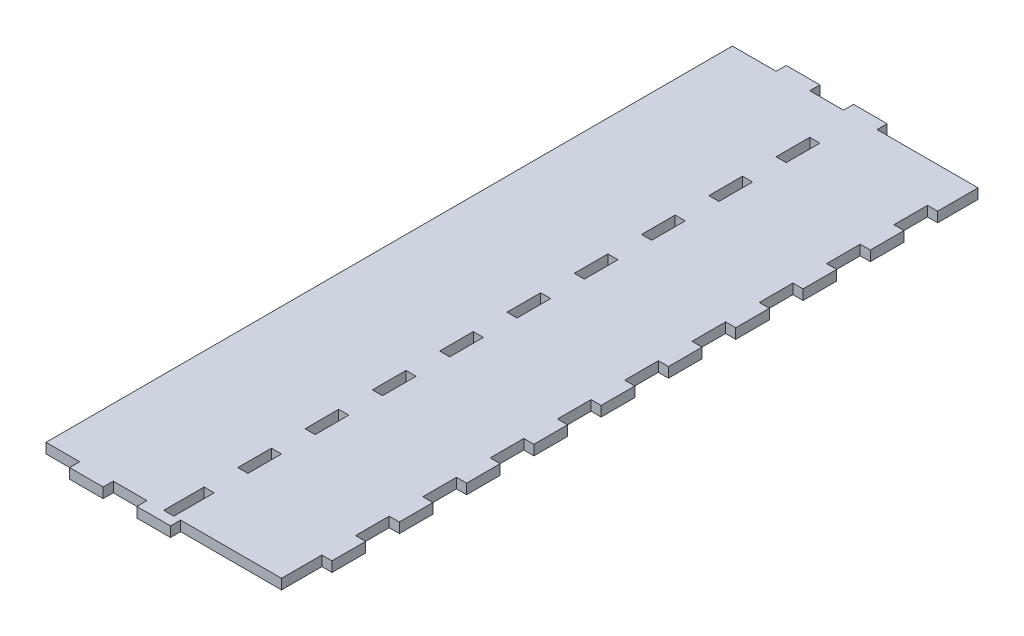
SolidWorks part; units mm, degrees
ref_plane "Front Plane" through (0, 0, 0) normal (0, 0, 1) x (1, 0, 0)
ref_plane "Top Plane" through (0, 0, 0) normal (0, 1, 0) x (1, 0, 0)
ref_plane "Right Plane" through (0, 0, 0) normal (1, 0, 0) x (0, 0, -1)
sketch "Sketch1" plane through (0, 0, 0) normal (0, 1, 0) x (1, 0, 0)
  line L1 (0, 0) -> (70, 0)
  line L2 (0, 0) -> (0, 204)
  line L3 (0, 204) -> (70, 204)
  line L4 (70, 0) -> (70, 204)
  dimension "D1" = 204
  dimension "D2" = 70
extrude "Boss-Extrude1" add sketch "Sketch1" along normal blind 3
sketch "Sketch2" plane through (70, 0, 0) normal (1, 0, 0) x (0, 0, -1)
  line L0 (0, 3) -> (204, 3) construction
  line L1 (204, 0) -> (192, 0)
  line L2 (204, 0) -> (204, 3)
  line L3 (204, 3) -> (192, 3)
  line L4 (192, 0) -> (192, 3)
  line L5 (0, 0) -> (204, 0) construction
  line L6 (182, 3) -> (172, 3)
  line L7 (182, 3) -> (182, 0)
  line L8 (182, 0) -> (172, 0)
  line L9 (172, 3) -> (172, 0)
  line L10 (162, 3) -> (162, 0)
  line L11 (162, 3) -> (152, 3)
  line L12 (152, 3) -> (152, 0)
  line L13 (162, 0) -> (152, 0)
  line L14 (142, 3) -> (142, 0)
  line L15 (142, 3) -> (132, 3)
  line L16 (132, 3) -> (132, 0)
  line L17 (142, 0) -> (132, 0)
  line L18 (122, 3) -> (122, 0)
  line L19 (122, 3) -> (112, 3)
  line L20 (112, 3) -> (112, 0)
  line L21 (122, 0) -> (112, 0)
  line L22 (102, 3) -> (102, 0)
  line L23 (102, 3) -> (92, 3)
  line L24 (92, 3) -> (92, 0)
  line L25 (102, 0) -> (92, 0)
  line L26 (82, 3) -> (82, 0)
  line L27 (82, 3) -> (72, 3)
  line L28 (72, 3) -> (72, 0)
  line L29 (82, 0) -> (72, 0)
  line L30 (62, 3) -> (62, 0)
  line L31 (62, 3) -> (52, 3)
  line L32 (52, 3) -> (52, 0)
  line L33 (62, 0) -> (52, 0)
  line L34 (42, 3) -> (42, 0)
  line L35 (42, 3) -> (32, 3)
  line L36 (32, 3) -> (32, 0)
  line L37 (42, 0) -> (32, 0)
  line L38 (22, 3) -> (22, 0)
  line L39 (22, 3) -> (12, 3)
  line L40 (12, 3) -> (12, 0)
  line L41 (22, 0) -> (12, 0)
  dimension "D1" = 12
  dimension "D2" = 10
  dimension "D3" = 10
  dimension "D4" = 9
extrude "Boss-Extrude2" add sketch "Sketch2" along normal blind 3
sketch "Esquisse4" plane through (0, 3, 0) normal (0, 1, 0) x (1, 0, 0)
  line L0 (73, 192) -> (70, 192) construction
  line L1 (35, 192) -> (38, 192)
  line L2 (35, 192) -> (35, 182)
  line L3 (35, 182) -> (38, 182)
  line L4 (38, 192) -> (38, 182)
  line L5 (73, 204) -> (0, 204) construction
  point P8 (36.5, 204)
  point P9 (36.5, 192)
  dimension "D1" = 3
  dimension "D2" = 10
extrude "Enlèv. mat.-Extru.3" cut sketch "Esquisse4" against normal through all
pattern_linear "Répétition linéaire2" count 10 spacing 20 along (0, 0, 1) of "Enlèv. mat.-Extru.3"
sketch "Esquisse5" plane through (0, 0, -2) normal (0, 0, -1) x (-1, 0, 0)
  line L0 (-38, 0) -> (-38, 3) construction
  line L1 (-38, 0) -> (-35, 0)
  line L2 (-38, 0) -> (-38, 3)
  line L3 (-38, 3) -> (-35, 3)
  line L4 (-35, 0) -> (-35, 3)
extrude "Enlèv. mat.-Extru.4" cut sketch "Esquisse5" against normal through all
sketch "Esquisse6" plane through (0, 0, 0) normal (0, 0, 1) x (1, 0, 0)
  line L0 (0, 0) -> (35, 0) construction
  line L1 (10, 0) -> (20, 0)
  line L2 (10, 0) -> (10, 3)
  line L3 (10, 3) -> (20, 3)
  line L4 (20, 0) -> (20, 3)
  line L5 (0, 3) -> (35, 3) construction
  line L6 (0, 3) -> (0, 0) construction
  line L7 (30, 0) -> (40, 0)
  line L8 (30, 0) -> (30, 3)
  line L9 (30, 3) -> (40, 3)
  line L10 (40, 0) -> (40, 3)
  line L16 (50, 0) -> (60, 0) [skipped]
  line L17 (50, 0) -> (50, 3) [skipped]
  line L18 (50, 3) -> (60, 3) [skipped]
  line L19 (60, 0) -> (60, 3) [skipped]
  dimension "D1" = 10
  dimension "D2" = 10
  dimension "D4" = 10
  dimension "D3" = 3
extrude "Boss.-Extru.1" add sketch "Esquisse6" along normal blind 3
sketch "Esquisse7" plane through (0, 0, -204) normal (0, 0, -1) x (-1, 0, 0)
  line L7 (-43, 0) -> (-33, 0)
  line L8 (-43, 0) -> (-43, 3)
  line L9 (-43, 3) -> (-33, 3)
  line L10 (-33, 0) -> (-33, 3)
  line L11 (-23, 0) -> (-13, 0)
  line L12 (-23, 0) -> (-23, 3)
  line L13 (-23, 3) -> (-13, 3)
  line L14 (-13, 0) -> (-13, 3)
  line L15 (0, 3) -> (0, 0) construction
  dimension "D1" = 13
  dimension "D2" = 10
  dimension "D3" = 10
extrude "Boss.-Extru.2" add sketch "Esquisse7" along normal blind 3
